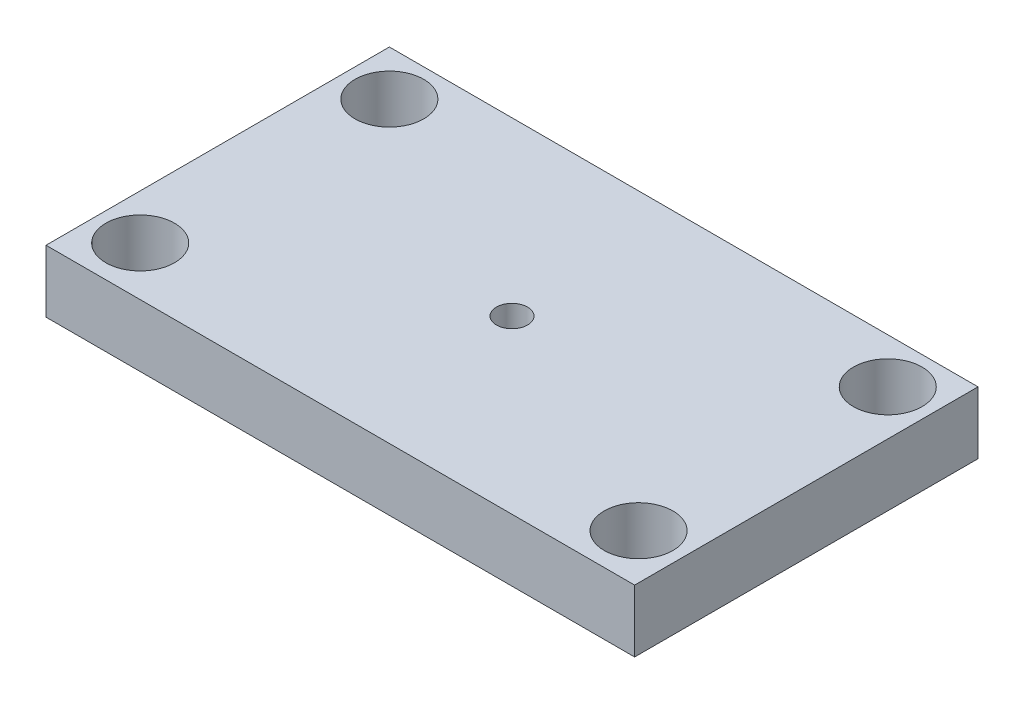
SolidWorks part; units mm, degrees
ref_plane "Front Plane" through (0, 0, 0) normal (0, 0, 1) x (1, 0, 0)
ref_plane "Top Plane" through (0, 0, 0) normal (0, 1, 0) x (1, 0, 0)
ref_plane "Right Plane" through (0, 0, 0) normal (1, 0, 0) x (0, 0, -1)
sketch "Sketch1" plane through (0, 0, 0) normal (0, 1, 0) x (1, 0, 0)
  line L0 (4.6, 30.4) -> (0, 30.4) construction
  line L1 (0, 0) -> (60, 0)
  line L2 (0, 0) -> (0, 35)
  line L3 (0, 35) -> (60, 35)
  line L4 (60, 0) -> (60, 35)
  line L5 (4.6, 30.4) -> (55.4, 30.4) construction
  line L6 (4.6, 30.4) -> (4.6, 5) construction
  line L7 (4.6, 5) -> (55.4, 5) construction
  line L8 (55.4, 30.4) -> (55.4, 5) construction
  line L9 (4.6, 30.4) -> (4.6, 35) construction
  circle A0 centre (4.6, 30.4) radius 3.5
  circle A1 centre (55.4, 30.4) radius 3.5
  circle A2 centre (4.6, 5) radius 3.5
  circle A3 centre (55.4, 5) radius 3.5
  circle A4 centre (30, 17.5) radius 1.5875
  point P13 (30, 30.4)
  point P14 (30, 35)
  point P20 (60, 17.5)
  dimension "D5" = 7
  dimension "D6" = 3.175
  dimension "D1" = 60
  dimension "D2" = 35
  dimension "D3" = 50.8
  dimension "D4" = 25.4
extrude "Boss-Extrude1" add sketch "Sketch1" along normal blind 6.35
